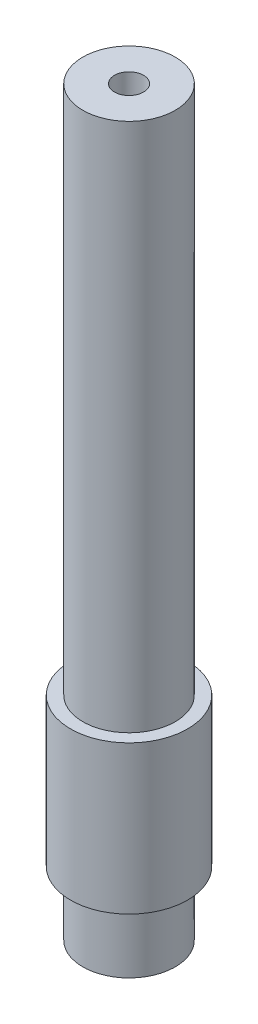
SolidWorks part; units mm, degrees
ref_plane "Płaszczyzna przednia" through (0, 0, 0) normal (0, 0, 1) x (1, 0, 0)
ref_plane "Płaszczyzna górna" through (0, 0, 0) normal (0, 1, 0) x (1, 0, 0)
ref_plane "Płaszczyzna prawa" through (0, 0, 0) normal (1, 0, 0) x (0, 0, -1)
sketch "Szkic1" plane through (0, 0, 0) normal (0, 0, 1) x (1, 0, 0)
  line L0 (-6.35, 0) -> (-2, 0)
  line L1 (0, -1.0935) -> (0, 112.2696) construction
  line L3 (-6.35, 0) -> (-6.35, 8.8054)
  line L4 (-6.35, 8.8054) -> (-8.05, 8.8054)
  line L5 (-8.05, 8.8054) -> (-8.05, 29.1946)
  line L6 (-8.05, 29.1946) -> (-6.35, 29.1946)
  line L7 (-6.35, 29.1946) -> (-6.35, 102)
  line L8 (-6.35, 102) -> (-2, 102)
  line L9 (-2, 102) -> (-2, 0)
  dimension "D1" = 102
  dimension "D3" = 12.7
  dimension "D4" = 16.1
  dimension "D5" = 4
revolve "Obrót2" add sketch "Szkic1" angle 360 about L1
